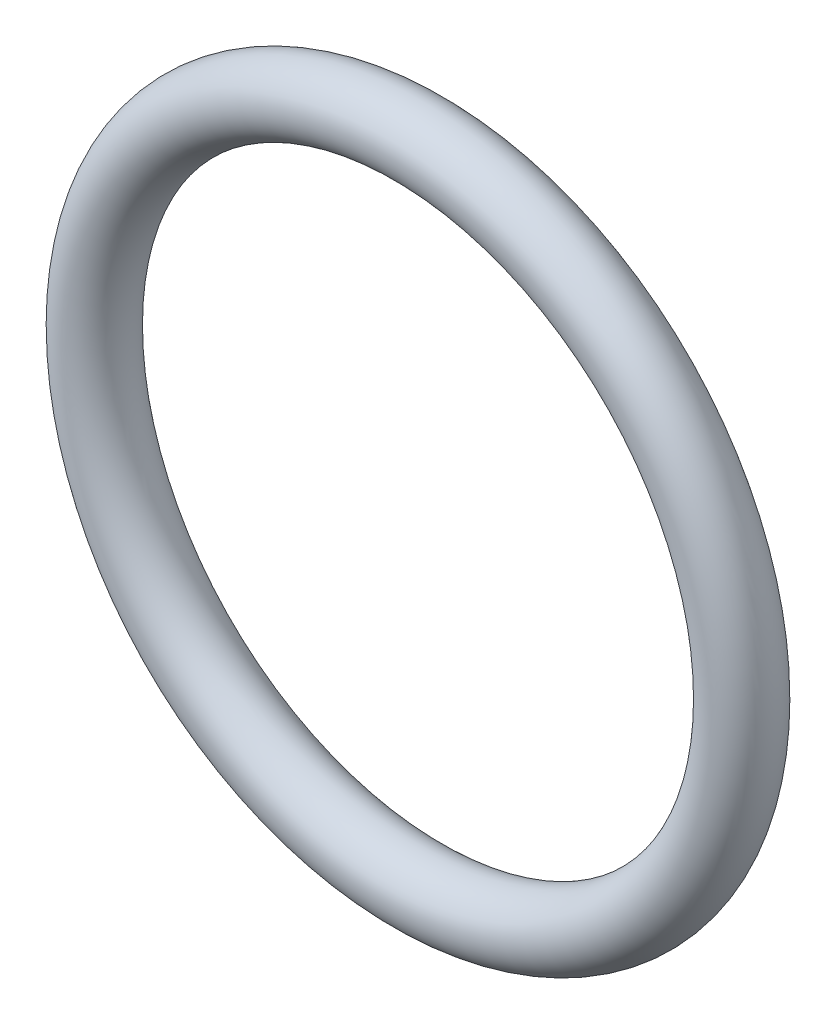
SolidWorks part; units mm, degrees
ref_plane "Front" through (0, 0, 0) normal (0, 0, 1) x (1, 0, 0)
ref_plane "Top" through (0, 0, 0) normal (0, 1, 0) x (1, 0, 0)
ref_plane "Right" through (0, 0, 0) normal (1, 0, 0) x (0, 0, -1)
sketch "Sketch1" plane through (0, 0, 0) normal (1, 0, 0) x (0, -1, 0)
  line L0 (0, -0.5) -> (0, 0.5) construction
  line L2 (-5.775, 0) -> (5.775, 0) construction
  line L3 (-4.25, 0) -> (4.25, 0) construction
  circle A0 centre (4.75, 0) radius 0.5
  point P9 (4.25, 0)
  point P10 (5.25, 0)
  point P13 (4.75, 0.5)
  point P14 (4.75, -0.5)
  dimension "Width" = 1
  dimension "ID" = 8.5
revolve "Revolve1" add sketch "Sketch1" angle 360 about L0
